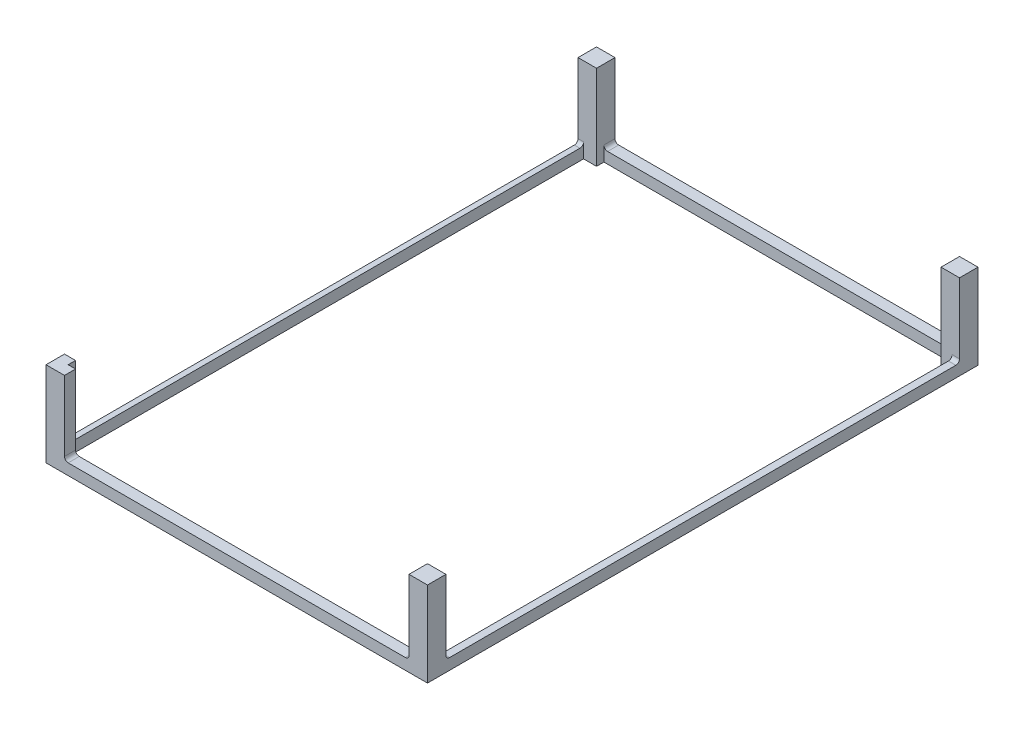
SolidWorks part; units mm, degrees
ref_plane "Front Plane" through (0, 0, 0) normal (0, 0, 1) x (1, 0, 0)
ref_plane "Top Plane" through (0, 0, 0) normal (0, 1, 0) x (1, 0, 0)
ref_plane "Right Plane" through (0, 0, 0) normal (1, 0, 0) x (0, 0, -1)
sketch "Sketch1" plane through (0, 0, 0) normal (0, 1, 0) x (1, 0, 0)
  line L2 (0, 0) -> (0, 149)
  line L5 (103.25, 149) -> (5, 149)
  line L9 (98.25, 146) -> (5, 146)
  line L10 (101.25, 144) -> (98.25, 144)
  line L11 (0, 149) -> (5, 149)
  line L12 (1.5, 144) -> (1.5, 5)
  line L13 (3, 5) -> (1.5, 5)
  line L14 (103.25, 0) -> (0, 0)
  line L15 (103.25, 0) -> (103.25, 149)
  line L16 (5, 3) -> (3, 3)
  line L17 (3, 3) -> (3, 5)
  line L21 (101.25, 5) -> (101.25, 144)
  line L22 (98.25, 144) -> (98.25, 146)
  line L23 (5, 3) -> (98.25, 3)
  line L24 (98.25, 3) -> (98.25, 5)
  line L25 (98.25, 5) -> (101.25, 5)
  line L26 (5, 146) -> (5, 144)
  line L27 (5, 144) -> (1.5, 144)
extrude "Boss-Extrude1" add sketch "Sketch1" along normal blind 3
sketch "Sketch2" plane through (0, 3, 0) normal (0, 1, 0) x (1, 0, 0)
  line L0 (0, 0) -> (5, 0)
  line L1 (98.25, 144) -> (103.25, 144)
  line L2 (98.25, 144) -> (98.25, 149)
  line L3 (98.25, 149) -> (103.25, 149)
  line L4 (103.25, 144) -> (103.25, 149)
  line L5 (0, 149) -> (5, 149)
  line L6 (0, 149) -> (0, 144)
  line L7 (0, 144) -> (5, 144)
  line L8 (5, 149) -> (5, 144)
  line L9 (98.25, 5) -> (103.25, 5)
  line L10 (98.25, 5) -> (98.25, 0)
  line L11 (98.25, 0) -> (103.25, 0)
  line L12 (103.25, 5) -> (103.25, 0)
  line L13 (0, 0) -> (103.25, 0) construction
  line L14 (5, 0) -> (5, 3)
  line L15 (3, 3) -> (98.25, 3) construction
  line L16 (5, 3) -> (3, 3)
  line L17 (3, 3) -> (3, 5)
  line L18 (3, 5) -> (0, 5)
  line L19 (0, 149) -> (0, 0) construction
  line L20 (0, 5) -> (0, 0)
extrude "Boss-Extrude2" add sketch "Sketch2" along normal blind 20
fillet "Fillet1" radius 1 8 edges at (5, 3, -1.5) (0.75, 3, -5) (98.25, 3, -1.5) (102.25, 3, -5) (98.25, 3, -147.5) (102.25, 3, -144) (5, 3, -147.5) (0.75, 3, -144)
